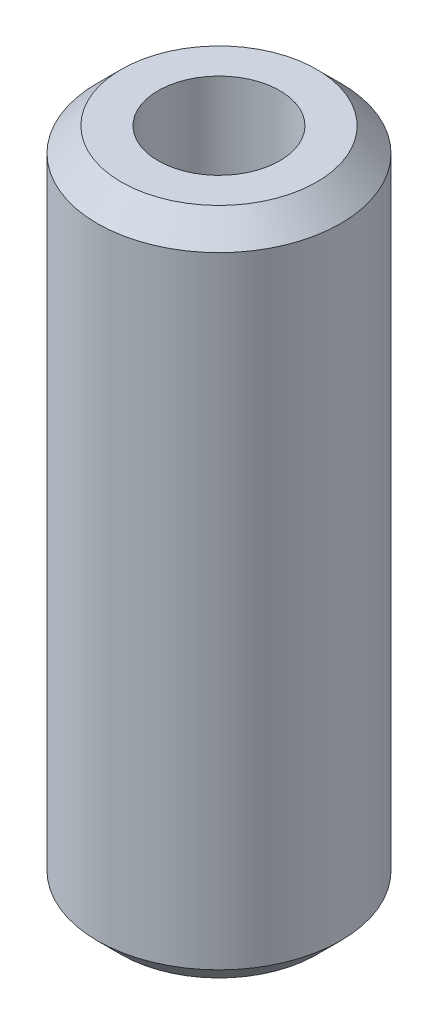
SolidWorks part; units mm, degrees
ref_plane "Front Plane" through (0, 0, 0) normal (0, 0, 1) x (1, 0, 0)
ref_plane "Top Plane" through (0, 0, 0) normal (0, 1, 0) x (1, 0, 0)
ref_plane "Right Plane" through (0, 0, 0) normal (1, 0, 0) x (0, 0, -1)
sketch "Sketch1" plane through (0, 0, 0) normal (0, 1, 0) x (1, 0, 0)
  circle A0 centre (0, 0) radius 6.35
  circle A1 centre (0, 0) radius 12.7
  dimension "D1" = 12.7
  dimension "D2" = 25.4
extrude "Boss-Extrude1" add sketch "Sketch1" along normal mid plane 69.85
chamfer "Chamfer1" distance 2.5 angle 45 2 edges at (0, 34.925, 12.7) (0, -34.925, 12.7)
